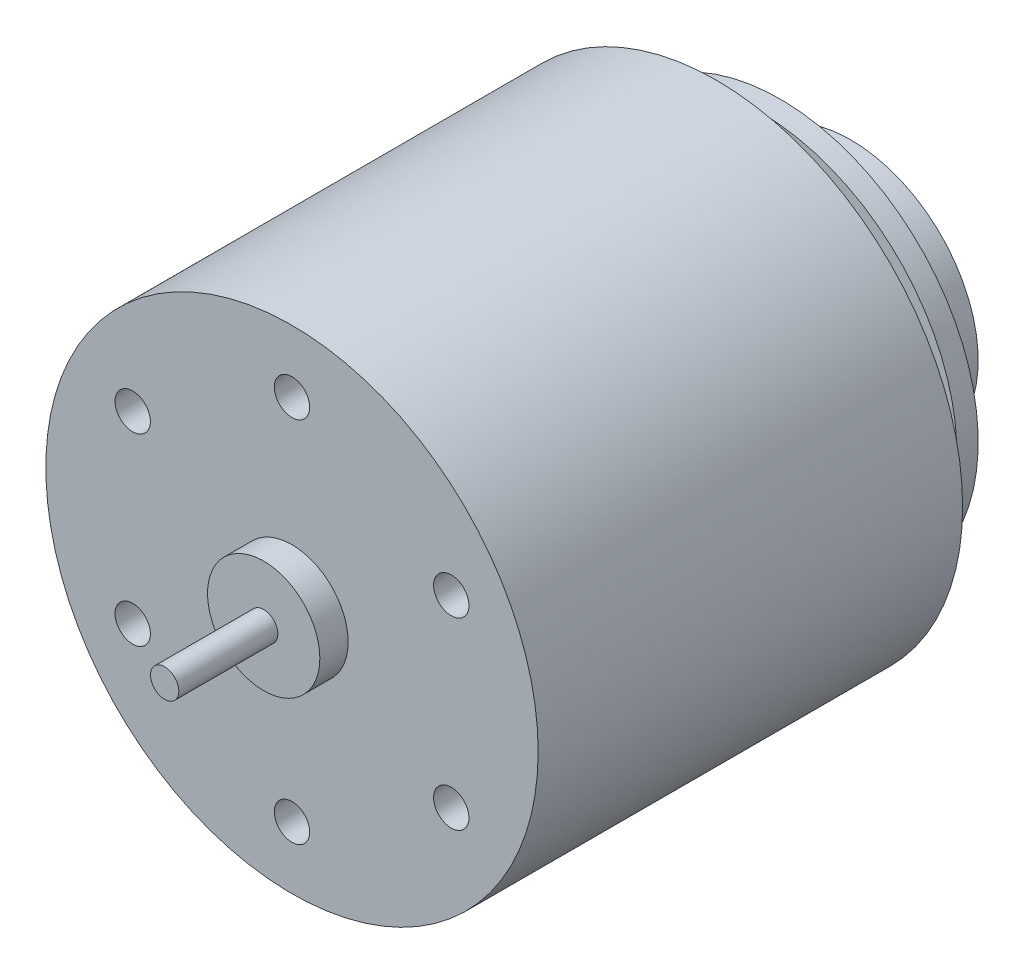
SolidWorks part; units mm, degrees
ref_plane "Front Plane" through (0, 0, 0) normal (0, 0, 1) x (1, 0, 0)
ref_plane "Top Plane" through (0, 0, 0) normal (0, 1, 0) x (1, 0, 0)
ref_plane "Right Plane" through (0, 0, 0) normal (1, 0, 0) x (0, 0, -1)
sketch "Sketch1" plane through (0, 0, 0) normal (0, 0, 1) x (1, 0, 0)
  circle A0 centre (0, 0) radius 18.4
  dimension "D1" = 36.8
extrude "Boss-Extrude1" add sketch "Sketch1" along normal blind 20
sketch "Sketch2" plane through (0, 0, 0) normal (0, 0, -1) x (-1, 0, 0)
  circle A0 centre (0, 0) radius 17.4
  dimension "D1" = 34.8
extrude "Boss-Extrude2" add sketch "Sketch2" along normal blind 30
sketch "Sketch3" plane through (0, 0, 20) normal (0, 0, 1) x (1, 0, 0)
  circle A0 centre (7, 0) radius 6
  dimension "D1" = 12
  dimension "D2" = 7
extrude "Boss-Extrude3" add sketch "Sketch3" along normal blind 6.5
fillet "Fillet1" radius 0.5 1 edges at (13, 0, 26.5)
sketch "Sketch4" plane through (0, 0, 26.5) normal (0, 0, 1) x (1, 0, 0)
  line L0 (7, -6.8172) -> (7, 7.1125) construction
  circle A0 centre (7, 0) radius 3
  dimension "D1" = 6
extrude "Boss-Extrude4" add sketch "Sketch4" along normal blind 15.5
sketch "Sketch5" plane through (0, 0, 42) normal (0, 0, 1) x (1, 0, 0)
  line L0 (5.5033, 2.6) -> (8.4967, 2.6)
  line L1 (7, -3) -> (9.3109, -3) construction
  circle A0 centre (7, 0) radius 3 construction
  circle A1 centre (7, 0) radius 3 construction
  arc A2 (8.4967, 2.6) -> (5.5033, 2.6) centre (7, 0) ccw
  dimension "D1" = 5.6
extrude "Cut-Extrude1" cut sketch "Sketch5" against normal blind 12
sketch "Sketch8" plane through (0, 0, 20) normal (0, 0, 1) x (1, 0, 0)
  line L0 (-0.5907, 0) -> (14.4711, 0) construction
  line L1 (7, 7.3586) -> (7, -7.457) construction
  arc A0 (10.1162, 7.3426) -> (10.1162, -7.3426) centre (0, 0) ccw
  arc A1 (10.1162, 7.3426) -> (10.1162, -7.3426) centre (6.9402, 0) ccw
  dimension "D1" = 25
  dimension "D2" = 16
extrude "Cut-Extrude2" cut sketch "Sketch8" against normal blind 1
sketch "Sketch9" plane through (0, 0, -30) normal (0, 0, -1) x (-1, 0, 0)
  circle A0 centre (0, 0) radius 4
  dimension "D1" = 8
extrude "Boss-Extrude5" add sketch "Sketch9" along normal blind 1
fillet "Fillet2" radius 0.5 1 edges at (-4, 0, -31)
ref_plane "Plane1" through (0, 0, -33) normal (0, 0, -1) x (-1, 0, 0)
sketch "Sketch10" plane through (0, 0, -33) normal (0, 0, -1) x (-1, 0, 0)
  circle A0 centre (0, 0) radius 14
  dimension "D1" = 28
extrude "Boss-Extrude6" add sketch "Sketch10" along normal blind 1.5 separate body
sketch "Sketch11" plane through (0, 0, -30) normal (0, 0, -1) x (-1, 0, 0)
  line L0 (0, 11.55) -> (0, 12.55) construction
  line L1 (-1.75, 12.55) -> (1.75, 12.55)
  line L2 (-1.75, 12.55) -> (-1.75, 11.55)
  line L3 (-1.75, 11.55) -> (1.75, 11.55)
  line L4 (1.75, 12.55) -> (1.75, 11.55)
  line L5 (-1.75, 12.05) -> (1.75, 12.05) construction
  line L6 (-3.5, 0) -> (3.5, 0) construction
  line L7 (1.75, -12.55) -> (1.75, -11.55)
  line L8 (-1.75, -12.55) -> (-1.75, -11.55)
  line L9 (-1.75, -12.55) -> (1.75, -12.55)
  line L10 (-1.75, -11.55) -> (1.75, -11.55)
  circle A0 centre (0, 0) radius 3.5 construction
  dimension "D1" = 3.5
  dimension "D2" = 1
  dimension "D3" = 12.05
extrude "Boss-Extrude7" add sketch "Sketch11" along normal blind 5.6
fillet "Fillet3" radius 0.5 4 edges at (-1.75, -12.05, -35.6) (1.75, -12.05, -35.6) (-1.75, 12.05, -35.6) (1.75, 12.05, -35.6)
ref_plane "Plane2" through (0, 0, -36.5) normal (0, 0, -1) x (-1, 0, 0)
sketch "Sketch13" plane through (0, 0, -36.5) normal (0, 0, -1) x (-1, 0, 0)
  circle A0 centre (0, 0) radius 9
  dimension "D1" = 18
extrude "Boss-Extrude8" add sketch "Sketch13" along normal blind 3 separate body
sketch "Sketch14" plane through (0, 0, -31) normal (0, 0, -1) x (-1, 0, 0)
  circle A0 centre (0, 0) radius 1.5
  dimension "D1" = 3
extrude "Boss-Extrude9" add sketch "Sketch14" along normal blind 8.55
fillet "Fillet4" radius 0.5 1 edges at (7, -3, 42)
sketch "Sketch15" plane through (0, 0, 42) normal (0, 0, 1) x (1, 0, 0)
  circle A0 centre (0, 0) radius 18.4
extrude "Cut-Extrude3" cut sketch "Sketch15" against normal up to surface (42 mm away) up to face at (17.4, 0, 0)
sketch "Sketch16" plane through (0, 0, 0) normal (0, 0, 1) x (1, 0, 0)
  circle A0 centre (0, 0) radius 3.9688
  dimension "D1" = 7.9375
extrude "Boss-Extrude10" add sketch "Sketch16" along normal blind 2 contours A0
sketch "Sketch17" plane through (0, 0, 2) normal (0, 0, 1) x (1, 0, 0)
  circle A0 centre (0, 0) radius 1
  dimension "D1" = 2
extrude "Boss-Extrude11" add sketch "Sketch17" along normal blind 7
sketch "Sketch18" plane through (0, 0, 0) normal (0, 0, 1) x (1, 0, 0)
  line L0 (0, 0) -> (0, 13) construction
  circle A0 centre (0, 13) radius 1.25
  dimension "D1" = 2.5
  dimension "D2" = 13
extrude "Cut-Extrude4" cut sketch "Sketch18" against normal blind 3
pattern_circular "CirPattern1" count 6 over 360 about axis through (0, 0, 0) along (0, 0, 1) of "Cut-Extrude4"
